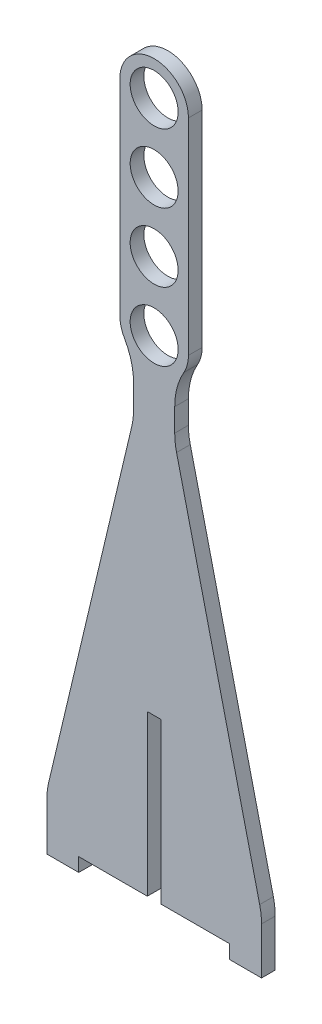
SolidWorks part; units mm, degrees
ref_plane "Plano frontal" through (0, 0, 0) normal (0, 0, 1) x (1, 0, 0)
ref_plane "Plano superior" through (0, 0, 0) normal (0, 1, 0) x (1, 0, 0)
ref_plane "Plano direito" through (0, 0, 0) normal (1, 0, 0) x (0, 0, -1)
sketch "Esboço1" plane through (0, 0, 0) normal (0, 0, 1) x (1, 0, 0)
  line L0 (-23.5, 0) -> (23.5, 0) construction
  line L1 (-23.5, 0) -> (-16.5, 0)
  line L2 (-16.5, 0) -> (-16.5, 3)
  line L3 (23.5, 0) -> (16.5, 0)
  line L4 (16.5, 0) -> (16.5, 3)
  line L5 (-16.5, 3) -> (16.5, 3)
  line L6 (-23.5, 0) -> (-23.5, 12)
  line L7 (23.5, 0) -> (23.5, 12)
  line L8 (-23.5, 12) -> (-4.5, 92)
  line L9 (-4.5, 92) -> (-4.5, 104)
  line L10 (23.5, 12) -> (4.5, 92)
  line L11 (4.5, 92) -> (4.5, 104)
  line L12 (-4.5, 104) -> (4.5, 104) construction
  line L13 (-7.5, 110) -> (-7.5, 155)
  line L14 (7.5, 110) -> (7.5, 155)
  arc A0 (4.5, 104) -> (7.5, 110) centre (0, 110) ccw
  circle A1 centre (0, 110) radius 5.25
  circle A2 centre (0, 125) radius 5.25
  arc A4 (-7.5, 110) -> (-4.5, 104) centre (0, 110) ccw
  circle A5 centre (0, 140) radius 5.25
  circle A6 centre (0, 155) radius 5.25
  arc A7 (-7.5, 155) -> (7.5, 155) centre (0, 155) cw
  point P3 (0, 104)
  point P4 (0, 0)
  dimension "D4" = 9
  dimension "D8" = 15
  dimension "D9" = 10.5
  dimension "D10" = 110
  dimension "D11" = 15
  dimension "D12" = 3
  dimension "D13" = 15
  dimension "D1" = 47
  dimension "D2" = 3
  dimension "D3" = 7
  dimension "D5" = 12
  dimension "D6" = 12
  dimension "D7" = 80
extrude "Ressalto-extrusão1" add sketch "Esboço1" along normal blind 3
fillet "Filete1" radius 15 6 edges at (23.5, 12, 1.5) (-23.5, 12, 1.5) (4.5, 92, 1.5) (4.5, 104, 1.5) (-4.5, 92, 1.5) (-4.5, 104, 1.5)
sketch "Esboço2" plane through (0, 0, 3) normal (0, 0, 1) x (1, 0, 0)
  line L0 (-16.5, 3) -> (16.5, 3) construction
  line L1 (1.5, 38) -> (-1.5, 38)
  line L2 (1.5, 38) -> (1.5, 3)
  line L3 (1.5, 3) -> (-1.5, 3)
  line L4 (-1.5, 38) -> (-1.5, 3)
  line L5 (1.5, 38) -> (-1.5, 3) construction
  line L6 (1.5, 3) -> (-1.5, 38) construction
  point P0 (0, 20.5)
  dimension "D1" = 3
  dimension "D2" = 35
extrude "Corte-extrusão1" cut sketch "Esboço2" against normal blind 3
